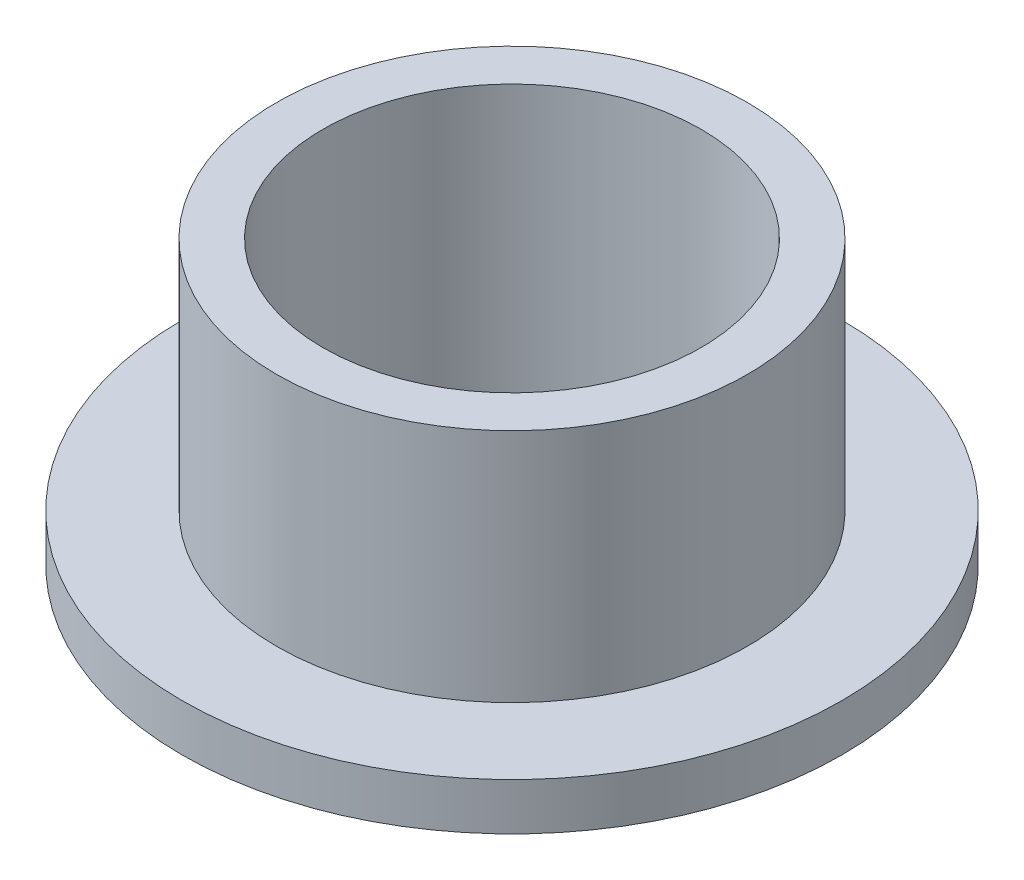
SolidWorks part; units mm, degrees
ref_plane "Front" through (0, 0, 0) normal (0, 0, 1) x (1, 0, 0)
ref_plane "Top" through (0, 0, 0) normal (0, 1, 0) x (1, 0, 0)
ref_plane "Right" through (0, 0, 0) normal (1, 0, 0) x (0, 0, -1)
sketch "Sketch1" plane through (0, 0, 0) normal (0, 1, 0) x (1, 0, 0)
  circle A0 centre (0, 0) radius 6.3754
  circle A1 centre (0, 0) radius 7.9375
  circle A2 centre (0, 0) radius 11.1125
  dimension "ID" = 12.7508
  dimension "OD" = 15.875
  dimension "FlangeOD" = 22.225
sketch "Sketch2" plane through (0, 0, 0) normal (0, 1, 0) x (1, 0, 0)
  circle A0 centre (0, 0) radius 6.3754 construction
  circle A1 centre (0, 0) radius 7.9375 construction
  circle A2 centre (0, 0) radius 6.3754
  circle A3 centre (0, 0) radius 7.9375
extrude "Boss-Extrude1" add sketch "Sketch2" along normal blind 9.525
sketch "Sketch3" plane through (0, 0, 0) normal (0, 1, 0) x (1, 0, 0)
  circle A0 centre (0, 0) radius 11.1125 construction
  circle A1 centre (0, 0) radius 7.9375 construction
  circle A2 centre (0, 0) radius 11.1125
  circle A3 centre (0, 0) radius 7.9375
extrude "Boss-Extrude2" add sketch "Sketch3" along normal blind 1.5875
